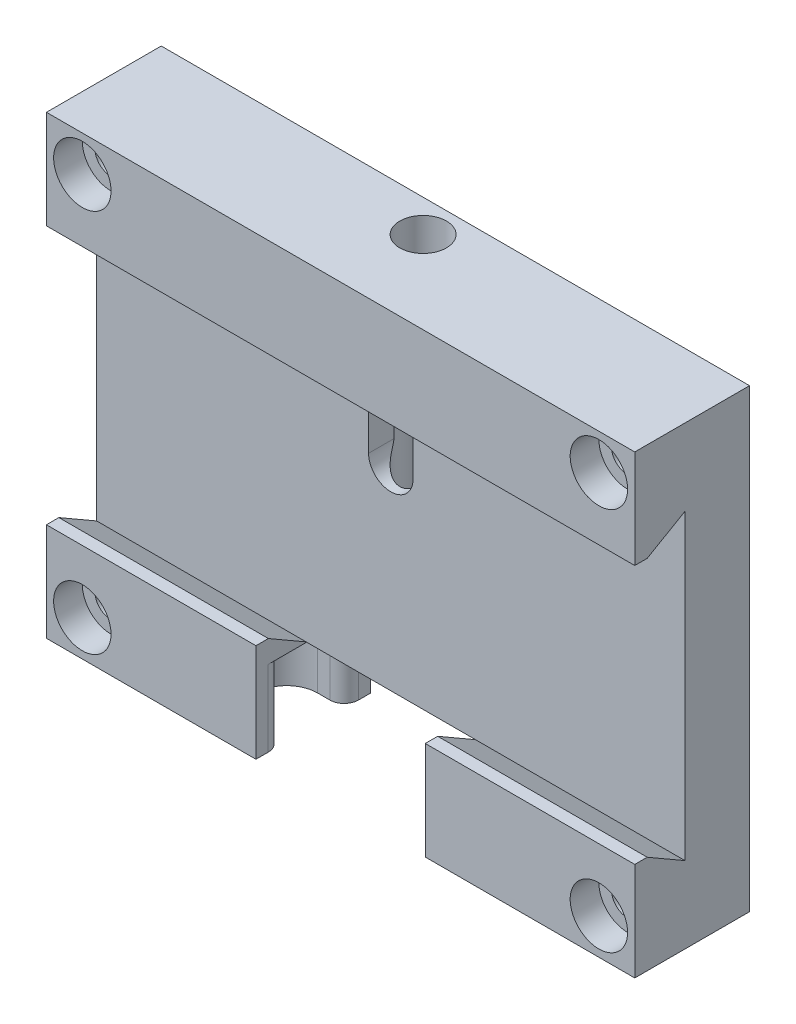
SolidWorks part; units mm, degrees
material "Сплав 2024"
ref_plane "Спереди" through (0, 0, 0) normal (0, 0, 1) x (1, 0, 0)
ref_plane "Сверху" through (0, 0, 0) normal (0, 1, 0) x (1, 0, 0)
ref_plane "Справа" through (0, 0, 0) normal (1, 0, 0) x (0, 0, -1)
sketch "Эскиз1" plane through (0, 0, 0) normal (0, 0, 1) x (1, 0, 0)
  line L1 (0, 0) -> (82, 0)
  line L2 (0, 0) -> (0, -63.5)
  line L3 (0, -63.5) -> (82, -63.5)
  line L4 (82, 0) -> (82, -63.5)
  dimension "D1" = 63.5
  dimension "D2" = 82
extrude "Бобышка-Вытянуть1" add sketch "Эскиз1" along normal blind 16
sketch "Эскиз2" plane through (0, 0, 0) normal (-1, 0, 0) x (0, 0, 1)
  line L0 (0, -31.75) -> (12.8711, -31.75) construction
  line L1 (0, 0) -> (0, -63.5) construction
  line L3 (16, 0) -> (16, -63.5) construction
  line L4 (9, -10.67) -> (16, -14.7115)
  line L5 (9, -10.67) -> (9, -52.83)
  line L6 (9, -52.83) -> (16, -48.7885)
  line L7 (16, -14.7115) -> (16, -48.7885)
  line L8 (9, -10.67) -> (16, -48.7885) construction
  line L9 (9, -52.83) -> (16, -14.7115) construction
  dimension "D1" = 42.16
  dimension "D2" = 60
  dimension "D3" = 60
  dimension "D4" = 7
extrude "Вырез-Вытянуть1" cut sketch "Эскиз2" against normal through all
ref_plane "Плоскость1" through (0, 0, 4) normal (0, 0, 1) x (1, 0, 0)
sketch "Эскиз3" plane through (0, 0, 4) normal (0, 0, 1) x (1, 0, 0)
  line L0 (0, -31.75) -> (82, -31.75) construction
  line L1 (0, -10.67) -> (0, -52.83) construction
  line L2 (82, -10.67) -> (82, -52.83) construction
  line L3 (41, 0) -> (41, -63.5) construction
  line L4 (82, 0) -> (0, 0) construction
  line L5 (0, -63.5) -> (82, -63.5) construction
  line L7 (41, -27.75) -> (82, -27.75)
  line L9 (41, -35.75) -> (82, -35.75)
  line L10 (82, -27.75) -> (82, -35.75)
  line L11 (41, -27.75) -> (82, -35.75) construction
  line L12 (41, -35.75) -> (82, -27.75) construction
  arc A0 (41, -27.75) -> (41, -35.75) centre (41, -31.75) ccw
  point P14 (61.5, -31.75)
  dimension "D1" = 8
sketch "Эскиз5" plane through (0, 0, 9) normal (0, 0, 1) x (1, 0, 0)
  line L0 (0, -31.75) -> (82, -31.75) construction
  line L1 (0, -31.75) -> (82, -31.75) construction
  line L2 (41, 0) -> (41, -63.5) construction
  line L3 (41, 0) -> (41, -63.5) construction
  line L4 (82, -10.67) -> (82, -52.83) construction
  line L5 (33, -27.75) -> (82, -27.75)
  line L7 (33, -35.75) -> (82, -35.75)
  line L8 (82, -27.75) -> (82, -35.75)
  line L9 (33, -27.75) -> (82, -35.75) construction
  line L10 (33, -35.75) -> (82, -27.75) construction
  arc A0 (33, -27.75) -> (33, -35.75) centre (33, -31.75) ccw
  point P6 (57.5, -31.75)
  dimension "D1" = 8
  dimension "D2" = 8
loft "Вырез-По сечениям1" [suppressed] cut profiles "Эскиз5", "Эскиз3"
sketch "Эскиз7" [suppressed] plane through (0, 0, 5) normal (0, 0, 1) x (1, 0, 0)
  line L0 (47.625, 0) -> (47.625, -63.5) construction
  line L1 (95.25, 0) -> (0, 0) construction
  line L2 (0, -63.5) -> (95.25, -63.5) construction
  line L3 (0, -31.75) -> (95.25, -31.75) construction
  line L4 (0, -13.2859) -> (0, -50.2141) construction
  line L5 (95.25, -35.75) -> (95.25, -27.75) construction
  line L6 (67.625, -24.8895) -> (67.625, -40.2612) construction
  line L7 (87.625, -24.8895) -> (87.625, -40.2612) construction
  line L8 (7.625, -24.8895) -> (7.625, -40.2612) construction
  line L9 (27.625, -24.8895) -> (27.625, -40.2612) construction
  circle A0 centre (27.625, -31.75) radius 4
  point P20 (27.625, -31.75)
  dimension "D3" = 8
  dimension "D1" = 20
  dimension "D2" = 20
extrude "Вырез-Вытянуть2" [suppressed] cut sketch "Эскиз7" along normal blind 5
hole_wizard "Отверстие обработанное метчиком M8x1.01" [suppressed] positions "Эскиз9" profile "Эскиз8" tap size "M8x1.0" standard "Ansi Metric"
sketch "Эскиз9" [suppressed] plane through (0, 0, 10) normal (0, 0, 1) x (1, 0, 0)
  line L0 (0, -31.75) -> (95.25, -31.75) construction
  line L1 (7.625, -24.8895) -> (7.625, -40.2612) construction
  line L2 (47.625, 0) -> (47.625, -63.5) construction
  line L3 (67.625, -24.8895) -> (67.625, -40.2612) construction
  line L4 (87.625, -24.8895) -> (87.625, -40.2612) construction
  point P0 (7.625, -31.75)
  point P2 (47.625, -31.75)
  point P4 (67.625, -31.75)
  point P6 (87.625, -31.75)
sketch "Эскиз8" plane through (7.625, -31.75, 10) normal (1, 0, 0) x (0, -1, 0)
  line L0 (0, 0) -> (0, 10)
  line L1 (0, 10) -> (3.5, 10)
  line L2 (3.5, 10) -> (3.5, 0)
  line L5 (3.5, 0) -> (0, 0)
  line L11 (0, -6.35) -> (0, 107.95) construction
  dimension "Диаметр проходного сверла" = 7
  dimension "Глубина проходного сверла" = 10
cosmetic thread "Отверстие резьбы1" [suppressed] parameters "D2"=8
cosmetic thread "Отверстие резьбы2" [suppressed] parameters "D2"=8
cosmetic thread "Отверстие резьбы3" [suppressed] parameters "D2"=8
cosmetic thread "Отверстие резьбы4" [suppressed] parameters "D2"=8
sketch "Эскиз10" [suppressed] plane through (0, 0, 10) normal (0, 0, 1) x (1, 0, 0)
  line L0 (90.25, -35.75) -> (95.25, -35.75)
  line L1 (95.25, -13.2859) -> (95.25, -27.75) construction
  line L2 (95.25, -27.75) -> (39.625, -27.75) construction
  line L3 (90.25, -27.75) -> (95.25, -27.75)
  line L4 (95.25, -27.75) -> (95.25, -22.75)
  line L5 (0, -31.75) -> (95.25, -31.75) construction
  line L6 (0, -31.75) -> (95.25, -31.75) construction
  line L7 (95.25, -35.75) -> (95.25, -40.75)
  arc A0 (90.25, -27.75) -> (95.25, -22.75) centre (90.25, -22.75) ccw
  arc A1 (90.25, -35.75) -> (95.25, -40.75) centre (90.25, -40.75) cw
  dimension "D1" = 5
  dimension "D2" = 5
extrude "Вырез-Вытянуть3" [suppressed] cut sketch "Эскиз10" against normal up to surface (5 mm away)
sketch "Эскиз11" plane through (0, 0, 0) normal (0, 0, -1) x (-1, 0, 0)
  line L0 (-82, -5) -> (0, -5) construction
  line L1 (-82, -63.5) -> (-82, 0) construction
  line L2 (0, 0) -> (0, -63.5) construction
  line L3 (-82, -58.5) -> (0, -58.5) construction
  line L4 (-82, 0) -> (0, 0) construction
  line L5 (0, -63.5) -> (-82, -63.5) construction
  line L8 (-82, -31.75) -> (0, -31.75) construction
  line L9 (-41, 0) -> (-41, -63.5) construction
  line L10 (-77, 0) -> (-77, -63.5) construction
  line L11 (-63.5, -11.75) -> (-18.5, -11.75) construction
  line L12 (-63.5, -11.75) -> (-63.5, -51.75) construction
  line L13 (-63.5, -51.75) -> (-18.5, -51.75) construction
  line L14 (-18.5, -11.75) -> (-18.5, -51.75) construction
  line L15 (-63.5, -11.75) -> (-18.5, -51.75) construction
  line L16 (-63.5, -51.75) -> (-18.5, -11.75) construction
  line L17 (-82, 0) -> (0, 0) construction
  line L18 (-82, -10.67) -> (-82, -52.83) construction
  line L19 (-5, 0) -> (-5, -63.5) construction
  line L20 (0, -10.67) -> (0, -52.83) construction
  line L21 (0, -63.5) -> (-82, -63.5) construction
  point P20 (-41, -31.75)
  dimension "D1" = 5
  dimension "D2" = 5
  dimension "D3" = 5
  dimension "D4" = 5
  dimension "D5" = 45
  dimension "D6" = 40
hole_wizard "Отверстие обработанное метчиком M4x0.71" [suppressed] positions "Эскиз13" profile "Эскиз12" tap size "M4x0.7" standard "Ansi Metric"
sketch "Эскиз13" plane through (0, 0, 0) normal (0, 0, -1) x (-1, 0, 0)
  line L0 (-80, -7) -> (0, -7) construction
  line L1 (-65, 0) -> (-65, -63.5) construction
  line L2 (-15, 0) -> (-15, -63.5) construction
  line L3 (-80, -56.5) -> (0, -56.5) construction
  point P0 (-65, -7)
  point P6 (-15, -7)
  point P10 (-15, -56.5)
  point P14 (-65, -56.5)
sketch "Эскиз12" plane through (65, -7, 0) normal (1, 0, 0) x (0, 1, 0)
  line L0 (0, 0) -> (0, 16)
  line L1 (0, 16) -> (1.65, 16)
  line L2 (1.65, 16) -> (1.65, 0)
  line L5 (1.65, 0) -> (0, 0)
  line L11 (0, -6.35) -> (0, 107.95) construction
  dimension "Диаметр проходного сверла" = 3.3
  dimension "Глубина проходного сверла" = 16
cosmetic thread "Отверстие резьбы5" [suppressed] parameters "D2"=4
cosmetic thread "Отверстие резьбы6" [suppressed] parameters "D2"=4
cosmetic thread "Отверстие резьбы7" [suppressed] parameters "D2"=4
cosmetic thread "Отверстие резьбы8" [suppressed] parameters "D2"=4
sketch "Эскиз15" plane through (0, 0, 16) normal (0, 0, 1) x (1, 0, 0)
  line L0 (41, 0) -> (41, -63.5) construction
  line L1 (82, 0) -> (0, 0) construction
  line L2 (0, -63.5) -> (82, -63.5) construction
  line L3 (82, -48.7885) -> (0, -48.7885) construction
  line L4 (29.2, -48.7885) -> (52.8, -48.7885)
  line L5 (29.2, -48.7885) -> (29.2, -63.5)
  line L6 (29.2, -63.5) -> (52.8, -63.5)
  line L7 (52.8, -48.7885) -> (52.8, -63.5)
  line L8 (29.2, -48.7885) -> (52.8, -63.5) construction
  line L9 (29.2, -63.5) -> (52.8, -48.7885) construction
  point P6 (41, -56.1443)
  dimension "D1" = 23.6
extrude "Вырез-Вытянуть4" cut sketch "Эскиз15" against normal up to surface (7 mm away) up to face at (41, -31.75, 9)
sketch "Эскиз16" plane through (0, 0, 9) normal (0, 0, 1) x (1, 0, 0)
  line L0 (41, 0) -> (41, -63.5) construction
  line L1 (29.2, -52.83) -> (52.8, -52.83)
  line L2 (29.2, -52.83) -> (29.2, -63.5)
  line L3 (29.2, -63.5) -> (52.8, -63.5)
  line L4 (52.8, -52.83) -> (52.8, -63.5)
  line L5 (29.2, -52.83) -> (52.8, -63.5) construction
  line L6 (29.2, -63.5) -> (52.8, -52.83) construction
  line L7 (29.2, -63.5) -> (52.8, -63.5) construction
  line L8 (82, -52.83) -> (52.8, -52.83) construction
  line L9 (52.8, -63.5) -> (52.8, -52.83) construction
  point P0 (41, -58.165)
extrude "Вырез-Вытянуть5" cut sketch "Эскиз16" against normal up to surface (9 mm away) up to face at (41, -31.75, 0)
sketch "Эскиз17" plane through (0, -52.83, 0) normal (0, -1, 0) x (1, 0, 0)
  line L0 (35.125, 5) -> (60.125, 5) construction
  line L3 (41, 9) -> (41, 0) construction
  line L4 (82, 9) -> (0, 9) construction
  line L5 (29.2, 0) -> (52.8, 0) construction
  circle A0 centre (33.5, 5) radius 2.5
  circle A1 centre (48.5, 5) radius 2.5
  dimension "D1" = 5
  dimension "D2" = 7.5
  dimension "D3" = 5
extrude "Вырез-Вытянуть6" cut sketch "Эскиз17" against normal blind 8
hole_wizard "Отверстие обработанное метчиком M4x0.72" positions "Эскиз19" profile "Эскиз18" tap size "M4x0.7" standard "Ansi Metric"
sketch "Эскиз19" plane through (0, -52.83, 0) normal (0, -1, 0) x (-1, 0, 0)
  line L0 (-41, -9) -> (-41, 0) construction
  line L1 (-35.125, -5) -> (-60.125, -5) construction
  point P0 (-41, -5)
sketch "Эскиз18" plane through (41, -52.83, 5) normal (1, 0, 0) x (0, 0, -1)
  line L0 (0, 0) -> (0, 10.9914)
  line L1 (0, 10.9914) -> (1.65, 10)
  line L2 (1.65, 10) -> (1.65, 0)
  line L5 (1.65, 0) -> (0, 0)
  line L10 (0, 10.9914) -> (-1.65, 10) construction
  line L11 (0, -6.35) -> (0, 107.95) construction
  dimension "Диаметр сверла" = 3.3
  dimension "Глубина сверла" = 10
  dimension "Угол заточки сверла" = 118
cosmetic thread "Отверстие резьбы9" parameters "D1"=8, "D2"=4
hole_wizard "Отверстие обработанное метчиком 3/8-161" [suppressed] positions "Эскиз21" profile "Эскиз20" tap size "3/8-16" standard "Ansi Inch"
sketch "Эскиз21" plane through (0, 0, 0) normal (0, 0, -1) x (-1, 0, 0)
  point P0 (-70.125, -11.75)
  point P3 (-70.125, -51.75)
  point P6 (-25.125, -51.75)
  point P9 (-25.125, -11.75)
sketch "Эскиз20" plane through (70.125, -11.75, 0) normal (1, 0, 0) x (0, 1, 0)
  line L0 (0, 0) -> (0, 10.3847)
  line L1 (0, 10.3847) -> (3.9687, 8)
  line L2 (3.9687, 8) -> (3.9687, 0)
  line L5 (3.9687, 0) -> (0, 0)
  line L10 (0, 10.3847) -> (-3.9688, 8) construction
  line L11 (0, -6.35) -> (0, 107.95) construction
  dimension "Диаметр сверла" = 7.9375
  dimension "Глубина сверла" = 8
  dimension "Угол заточки сверла" = 118
cosmetic thread "Отверстие резьбы10" [suppressed] parameters "D1"=8, "D2"=9.525
cosmetic thread "Отверстие резьбы11" [suppressed] parameters "D1"=8, "D2"=9.525
cosmetic thread "Отверстие резьбы12" [suppressed] parameters "D1"=8, "D2"=9.525
cosmetic thread "Отверстие резьбы13" [suppressed] parameters "D1"=8, "D2"=9.525
chamfer "Фаска1" [suppressed] distance 4 angle 45
hole_wizard "Отверстие обработанное метчиком 1/4-201" [suppressed] positions "Эскиз23" profile "Эскиз22" tap size "1/4-20" standard "Ansi Inch"
sketch "Эскиз23" plane through (0, 0, 0) normal (0, 0, -1) x (-1, 0, 0)
  point P0 (-25.125, -51.75)
  point P3 (-25.125, -11.75)
  point P6 (-70.125, -11.75)
  point P9 (-70.125, -51.75)
sketch "Эскиз22" plane through (25.125, -51.75, 0) normal (1, 0, 0) x (0, 1, 0)
  line L0 (0, 0) -> (0, 10.5338)
  line L1 (0, 10.5338) -> (2.5527, 9)
  line L2 (2.5527, 9) -> (2.5527, 0)
  line L5 (2.5527, 0) -> (0, 0)
  line L10 (0, 10.5338) -> (-2.5527, 9) construction
  line L11 (0, -6.35) -> (0, 107.95) construction
  dimension "Диаметр сверла" = 5.1054
  dimension "Глубина сверла" = 9
  dimension "Угол заточки сверла" = 118
cosmetic thread "Отверстие резьбы14" [suppressed] parameters "D1"=9, "D2"=6.35
cosmetic thread "Отверстие резьбы15" [suppressed] parameters "D1"=9, "D2"=6.35
cosmetic thread "Отверстие резьбы16" [suppressed] parameters "D1"=9, "D2"=6.35
cosmetic thread "Отверстие резьбы17" [suppressed] parameters "D1"=9, "D2"=6.35
sketch "Эскиз25" plane through (0, 0, 9) normal (0, 0, 1) x (1, 0, 0)
  line L0 (41, 0) -> (41, -52.83) construction
  line L1 (82, 0) -> (0, 0) construction
  line L2 (52.8, -52.83) -> (29.2, -52.83) construction
  line L3 (41, -18.7115) -> (41, -25.7115) construction
  line L4 (44.1, -18.7115) -> (44.1, -25.7115)
  line L5 (37.9, -18.7115) -> (37.9, -25.7115)
  line L6 (82, -14.7115) -> (0, -14.7115) construction
  arc A0 (44.1, -18.7115) -> (37.9, -18.7115) centre (41, -18.7115) ccw
  arc A1 (37.9, -25.7115) -> (44.1, -25.7115) centre (41, -25.7115) ccw
  point P8 (41, -22.2115)
  dimension "D1" = 3.1
  dimension "D2" = 4
  dimension "D3" = 7
extrude "Вырез-Вытянуть7" cut sketch "Эскиз25" against normal blind 4
sketch "Эскиз26" plane through (0, 0, 0) normal (0, 1, 0) x (1, 0, 0)
  line L0 (0, -9) -> (82, -9) construction
  line L1 (0, -16) -> (0, 0) construction
  line L2 (82, -16) -> (82, 0) construction
  line L4 (82, 0) -> (0, 0) construction
  line L5 (41, 0) -> (41, -16) construction
  line L6 (82, -16) -> (0, -16) construction
  circle A0 centre (41, -4.5) radius 3.25
  dimension "D2" = 6.5
  dimension "D1" = 9
  dimension "D3" = 4.5
extrude "Вырез-Вытянуть8" cut sketch "Эскиз26" against normal blind 38
sketch "Эскиз27" plane through (0, 0, 0) normal (0, 0, -1) x (-1, 0, 0)
  line L0 (-82, 0) -> (0, 0) construction
  line L1 (-82, 0) -> (-72, 0)
  line L2 (-82, 0) -> (-82, -63.5)
  line L3 (-82, -63.5) -> (-72, -63.5)
  line L4 (-72, 0) -> (-72, -63.5)
  line L5 (-52.8, -63.5) -> (-82, -63.5) construction
  line L7 (-41, 0) -> (-41, -63.5) construction
  line L8 (-82, -63.5) -> (-82, 0) construction
  line L9 (0, -63.5) -> (-10, -63.5)
  line L10 (0, 0) -> (0, -63.5)
  line L11 (0, 0) -> (-10, 0)
  line L12 (-10, 0) -> (-10, -63.5)
  dimension "D1" = 10
extrude "Вырез-Вытянуть9" [suppressed] cut sketch "Эскиз27" against normal blind 5
hole_wizard "Цековка для винта с внутренним шестигранником M41" positions "Эскиз29" profile "Эскиз28" counterbore size "M4" standard "Ansi Metric" end condition through all
sketch "Эскиз29" plane through (30.7592, 26.7934, 16) normal (0, 0, -1) x (-1, 0, 0)
  line L0 (-51.2408, -31.7934) -> (30.7592, -31.7934) construction
  line L1 (-46.2408, -26.7934) -> (-46.2408, -90.2934) construction
  line L2 (-51.2408, -85.2934) -> (30.7592, -85.2934) construction
  line L3 (25.7592, -26.7934) -> (25.7592, -90.2934) construction
  point P0 (-46.2408, -31.7934)
  point P6 (-46.2408, -85.2934)
  point P10 (25.7592, -85.2934)
  point P14 (25.7592, -31.7934)
sketch "Эскиз28" plane through (77, -5, 16) normal (1, 0, 0) x (0, -1, 0)
  line L0 (0, 0) -> (0, 16)
  line L1 (0, 16) -> (2.25, 16)
  line L3 (2.25, 16) -> (2.25, 4)
  line L4 (2.25, 4) -> (4, 4)
  line L5 (4, 4) -> (4, 0)
  line L7 (4, 0) -> (0, 0)
  line L11 (0, -6.35) -> (0, 107.95) construction
  dimension "Диаметр сквозного отверстия" = 4.5
  dimension "Глубина сквозного отверстия" = 16
  dimension "Диаметр цековки" = 8
  dimension "Глубина цековки" = 4
chamfer "Фаска2" distance 1 angle 90 3 edges at (67.4, -48.7885, 16) (14.6, -48.7885, 16) (41, -14.7115, 16)
sketch "Эскиз32" plane through (0, -63.5, 0) normal (0, -1, 0) x (1, 0, 0)
  line L0 (29.5, 12.3) -> (25.5, 12.3)
  line L1 (41, 9) -> (41, 0) construction
  line L2 (52.8, 9) -> (29.2, 9) construction
  line L3 (25.5, 3.7) -> (29.5, 3.7)
  line L4 (29.2, 8) -> (52.8, 8) construction
  line L5 (52.5, 3.9) -> (56.5, 3.9) construction
  line L6 (56.5, 12.1) -> (52.5, 12.1) construction
  line L7 (29.2, 0) -> (29.2, 16) construction
  line L8 (52.8, 0) -> (52.8, 9) construction
  line L9 (52.5, 3.7) -> (56.5, 3.7)
  line L10 (29.5, 12.1) -> (25.5, 12.1) construction
  line L11 (25.5, 3.9) -> (29.5, 3.9) construction
  line L12 (56.5, 12.3) -> (52.5, 12.3)
  line L13 (29.5, 12.3) -> (29.5, 3.7)
  line L14 (52.5, 12.3) -> (52.5, 3.7)
  arc A0 (56.5, 3.9) -> (56.5, 12.1) centre (56.5, 8) ccw construction
  arc A1 (25.5, 12.1) -> (25.5, 3.9) centre (25.5, 8) ccw construction
  arc A2 (25.5, 12.3) -> (25.5, 3.7) centre (25.5, 8) ccw
  arc A3 (56.5, 3.7) -> (56.5, 12.3) centre (56.5, 8) ccw
  point P20 (41, 0)
  dimension "D1" = 0.2
extrude "Вырез-Вытянуть12" cut sketch "Эскиз32" against normal blind 10.6
fillet "Скругление1" radius 2 4 edges at (52.8, -58.2, 12.3) (52.8, -58.2, 3.7) (29.2, -58.2, 3.7) (29.2, -58.2, 12.3)
